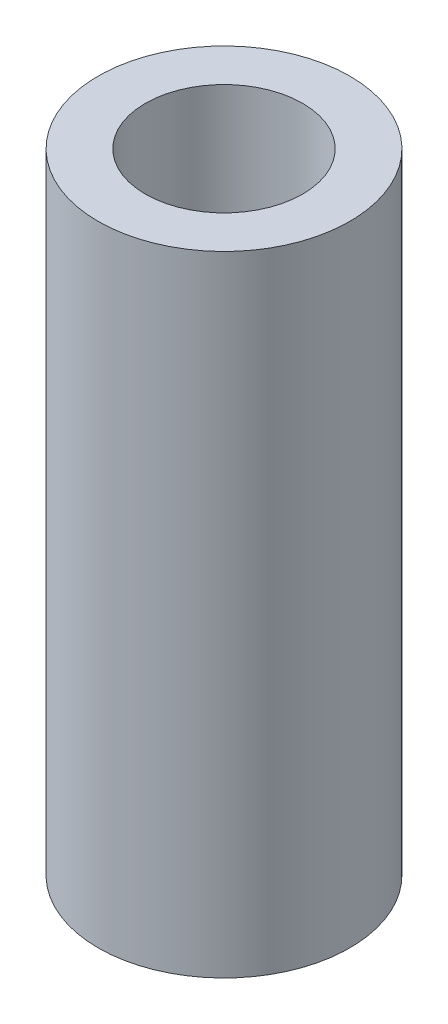
SolidWorks part; units mm, degrees
ref_plane "Front Plane" through (0, 0, 0) normal (0, 0, 1) x (1, 0, 0)
ref_plane "Top Plane" through (0, 0, 0) normal (0, 1, 0) x (1, 0, 0)
ref_plane "Right Plane" through (0, 0, 0) normal (1, 0, 0) x (0, 0, -1)
sketch "Sketch2" plane through (0, 0, 0) normal (0, 1, 0) x (1, 0, 0)
  circle A0 centre (0, 0) radius 4
  circle A1 centre (0, 0) radius 2.5
extrude "Boss-Extrude1" add sketch "Sketch2" along normal blind 20 contours A0 | A1
